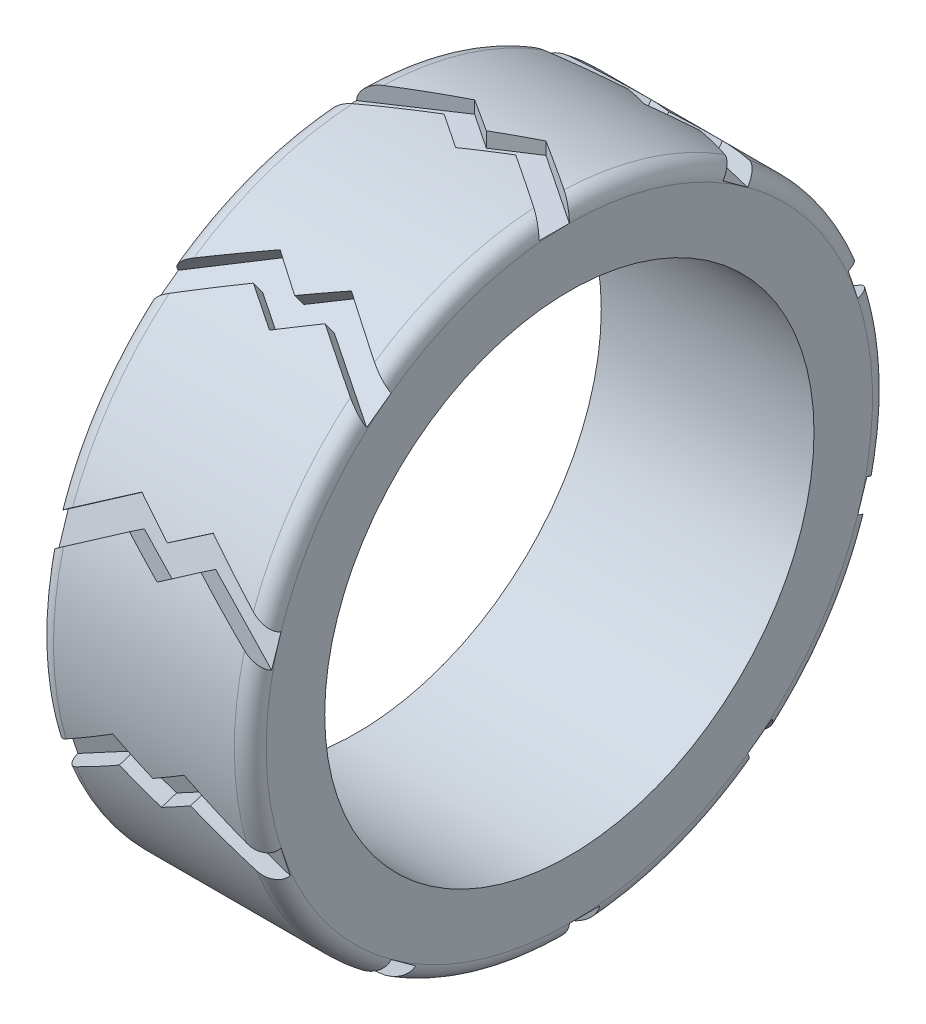
SolidWorks part; units mm, degrees
ref_plane "Front Plane" through (0, 0, 0) normal (0, 0, 1) x (1, 0, 0)
ref_plane "Top Plane" through (0, 0, 0) normal (0, 1, 0) x (1, 0, 0)
ref_plane "Right Plane" through (0, 0, 0) normal (1, 0, 0) x (0, 0, -1)
sketch "Sketch1" plane through (0, 0, 0) normal (0, 1, 0) x (1, 0, 0)
  line L0 (0, 0) -> (-10, 0) construction
  line L1 (-10, 15) -> (0, 15)
  line L2 (-10, 11.5) -> (0, 11.5)
  line L3 (-10, 15) -> (-10, 11.5)
  line L4 (0, 15) -> (0, 11.5)
  dimension "D1" = 10
  dimension "D2" = 15
  dimension "D3" = 3.5
revolve "Revolve1" add sketch "Sketch1" angle 360 about L0
fillet "Fillet1" radius 0.75 1 edges at (0, 0, -15)
fillet "Fillet2" radius 0.75 1 edges at (-10, 0, -15)
ref_plane "Plane3" through (0, 15, 0) normal (0, 1, 0) x (1, 0, 0)
sketch "Sketch3" plane through (0, 15, 0) normal (0, 1, 0) x (1, 0, 0)
  line L0 (-10, 0) -> (-6.6685, 2.2164)
  line L1 (-10, 14.25) -> (-10, -14.25) construction
  line L2 (0, 0) -> (-3.3175, 2.2164)
  line L3 (-3.3175, 2.2164) -> (-5.0123, 1.1082)
  line L4 (-5.0123, 1.1082) -> (-6.6685, 2.2164)
  line L5 (-10, 0) -> (-10, -1.4426)
  line L6 (-10, -1.4426) -> (-6.6685, 0.7738)
  line L7 (-6.6685, 0.7738) -> (-5.0123, -0.3327)
  line L8 (-5.0123, -0.3327) -> (-3.3175, 0.7948)
  line L9 (-3.3175, 0.7948) -> (0, -1.4217)
  line L10 (0, -14.25) -> (0, 14.25) construction
  line L11 (0, -1.4217) -> (0, 0)
extrude "Cut-Extrude2" cut sketch "Sketch3" against normal blind 0.75
pattern_circular "CirPattern1" count 10 every 36 about axis through (0, 0, 0) along (1, 0, 0) of "Cut-Extrude2"
